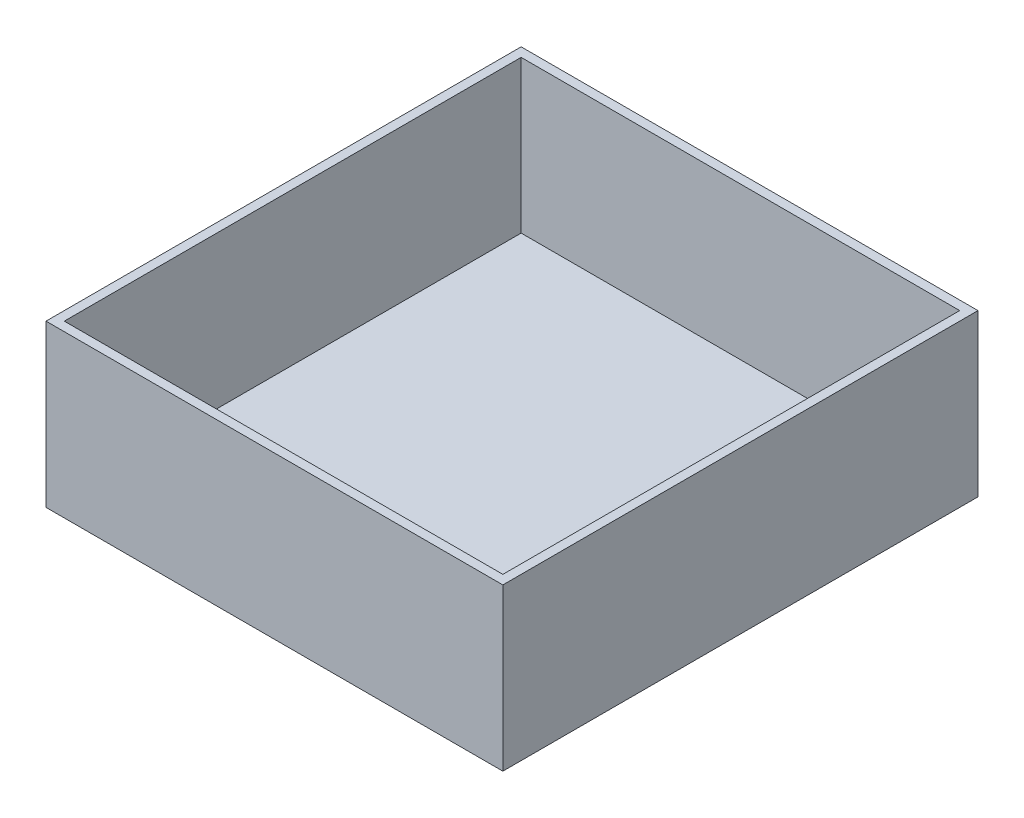
SolidWorks part; units mm, degrees
ref_plane "Front Plane" through (0, 0, 0) normal (0, 0, 1) x (1, 0, 0)
ref_plane "Top Plane" through (0, 0, 0) normal (0, 1, 0) x (1, 0, 0)
ref_plane "Right Plane" through (0, 0, 0) normal (1, 0, 0) x (0, 0, -1)
sketch "Sketch1" plane through (0, 0, 0) normal (0, 1, 0) x (1, 0, 0)
  line L1 (-79.375, -82.55) -> (79.375, -82.55)
  line L2 (-79.375, -82.55) -> (-79.375, 82.55)
  line L3 (-79.375, 82.55) -> (79.375, 82.55)
  line L4 (79.375, -82.55) -> (79.375, 82.55)
  line L5 (-79.375, -82.55) -> (79.375, 82.55) construction
  line L6 (-79.375, 82.55) -> (79.375, -82.55) construction
  point P0 (0, 0)
  dimension "D1" = 165.1
  dimension "D2" = 158.75
extrude "Boss-Extrude1" add sketch "Sketch1" along normal blind 3.175
sketch "Sketch2" plane through (0, 3.175, 0) normal (0, 1, 0) x (1, 0, 0)
  line L8 (76.2, -79.375) -> (76.2, 79.375)
  line L9 (76.2, 79.375) -> (-76.2, 79.375)
  line L10 (-76.2, 79.375) -> (-76.2, -79.375)
  line L11 (-76.2, -79.375) -> (76.2, -79.375)
  line L12 (76.2, -79.375) -> (76.2, 79.375)
  line L13 (76.2, 79.375) -> (-76.2, 79.375)
  line L14 (-76.2, 79.375) -> (-76.2, -79.375)
  line L15 (-76.2, -79.375) -> (76.2, -79.375)
  line L16 (79.375, -82.55) -> (79.375, 82.55)
  line L17 (79.375, 82.55) -> (-79.375, 82.55)
  line L18 (-79.375, 82.55) -> (-79.375, -82.55)
  line L19 (-79.375, -82.55) -> (79.375, -82.55)
  line L20 (79.375, -82.55) -> (79.375, 82.55)
  line L21 (79.375, 82.55) -> (-79.375, 82.55)
  line L22 (-79.375, 82.55) -> (-79.375, -82.55)
  line L23 (-79.375, -82.55) -> (79.375, -82.55)
  dimension "D1" = 3.175
  dimension "D2" = 0
extrude "Boss-Extrude2" add sketch "Sketch2" along normal blind 52.8828
